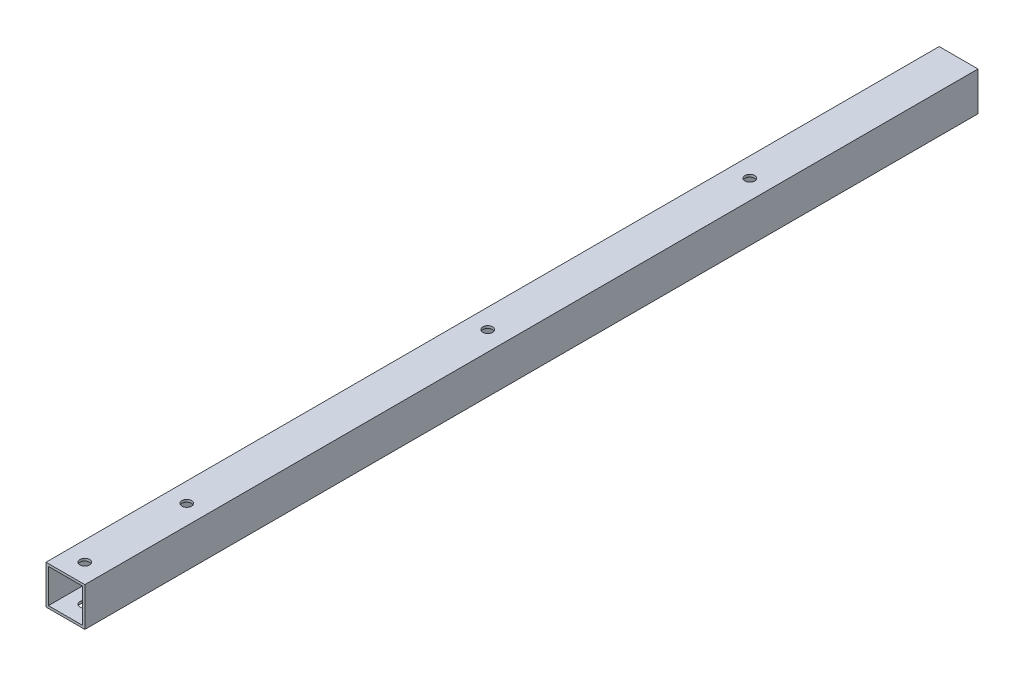
SolidWorks part; units mm, degrees
ref_plane "Front Plane" through (0, 0, 0) normal (0, 0, 1) x (1, 0, 0)
ref_plane "Top Plane" through (0, 0, 0) normal (0, 1, 0) x (1, 0, 0)
ref_plane "Right Plane" through (0, 0, 0) normal (1, 0, 0) x (0, 0, -1)
sketch "Sketch1" plane through (0, 0, 0) normal (0, 0, 1) x (1, 0, 0)
  line L0 (-536.575, 327.025) -> (-492.125, 327.025)
  line L1 (-539.75, 330.2) -> (-488.95, 330.2)
  line L2 (-539.75, 330.2) -> (-539.75, 279.4)
  line L3 (-539.75, 279.4) -> (-488.95, 279.4)
  line L4 (-488.95, 330.2) -> (-488.95, 279.4)
  line L5 (-492.125, 327.025) -> (-492.125, 282.575)
  line L6 (-536.575, 282.575) -> (-492.125, 282.575)
  line L7 (-536.575, 327.025) -> (-536.575, 282.575)
  line L8 (-584.2, 279.4) -> (-468.774, 279.4) construction
  line L10 (-584.2, -304.8) -> (-584.2, 304.8) construction
  circle A0 centre (-584.2, 304.8) radius 25.4 construction
  circle A1 centre (-584.2, 304.8) radius 25.4 construction
  dimension "D1" = 3.175
  dimension "D2" = 50.8
  dimension "D3" = 44.45
extrude "Extrude1" add sketch "Sketch1" along normal blind 1117.6 and the other way blind 50.8
sketch "Sketch2" plane through (-539.75, 0, 0) normal (-1, 0, 0) x (0, 0, 1)
  line L0 (1117.6, 330.2) -> (1066.8, 279.4)
  line L1 (-50.8, 279.4) -> (1117.6, 279.4) construction
  line L2 (1066.8, 279.4) -> (1117.6, 279.4)
  line L3 (1117.6, 279.4) -> (1117.6, 330.2)
extrude "Cut-Extrude1" [suppressed] cut sketch "Sketch2" against normal through all
sketch "Sketch3" plane through (0, 330.2, 0) normal (0, 1, 0) x (1, 0, 0)
  line L0 (-488.95, -1117.6) -> (-539.75, -1117.6) construction
  line L1 (-514.35, -1117.6) -> (-514.35, -1092.2) construction
  circle A0 centre (-514.35, -1092.2) radius 6.35
  circle A1 centre (-514.35, -958.85) radius 6.35
  circle A2 centre (-514.35, -565.15) radius 6.35
  circle A3 centre (-514.35, -222.25) radius 6.35
  dimension "D2" = 12.7
  dimension "D3" = 12.7
  dimension "D1" = 25.4
extrude "Cut-Extrude2" cut sketch "Sketch3" against normal through all
